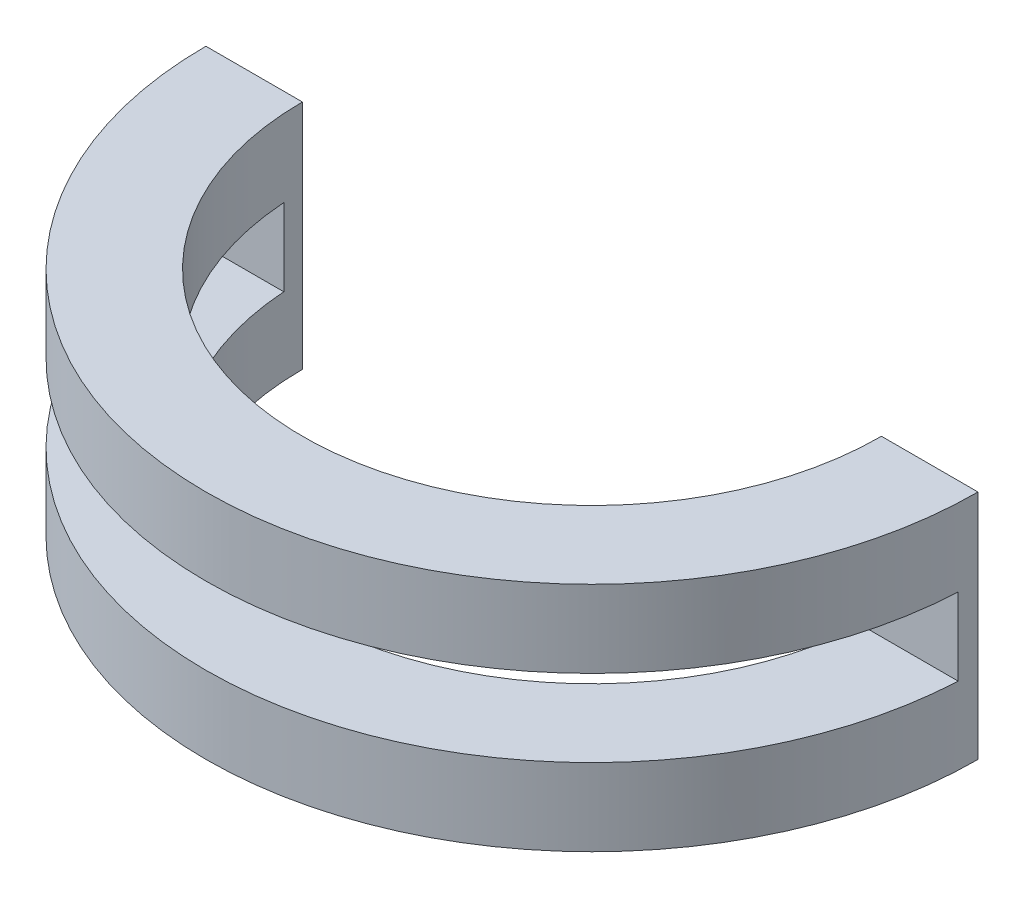
SolidWorks part; units mm, degrees
ref_plane "Front Plane" through (0, 0, 0) normal (0, 0, 1) x (1, 0, 0)
ref_plane "Top Plane" through (0, 0, 0) normal (0, 1, 0) x (1, 0, 0)
ref_plane "Right Plane" through (0, 0, 0) normal (1, 0, 0) x (0, 0, -1)
sketch "Sketch2" plane through (0, 0, 0) normal (0, 1, 0) x (1, 0, 0)
  line L1 (-100, 0) -> (-75, 0)
  line L2 (75, 0) -> (100, 0)
  arc A0 (-75, 0) -> (75, 0) centre (0, 0) ccw
  arc A1 (-100, 0) -> (100, 0) centre (0, 0) ccw
  dimension "D1" = 75
  dimension "D2" = 100
extrude "Boss-Extrude1" add sketch "Sketch2" along normal blind 60
ref_plane "Plane1" through (0, 30, 0) normal (0, 1, 0) x (1, 0, 0)
sketch "Sketch4" plane through (0, 30, 0) normal (0, 1, 0) x (1, 0, 0)
  line L4 (-99.8749, -5) -> (-74.8331, -5)
  line L5 (74.8331, -5) -> (99.8749, -5)
  arc A4 (-99.8749, -5) -> (99.8749, -5) centre (0, 0) ccw
  arc A5 (-74.8331, -5) -> (74.8331, -5) centre (0, 0) ccw
  dimension "D1" = 5
extrude "Cut-Extrude4" cut sketch "Sketch4" against normal blind 10 and the other way blind 10
